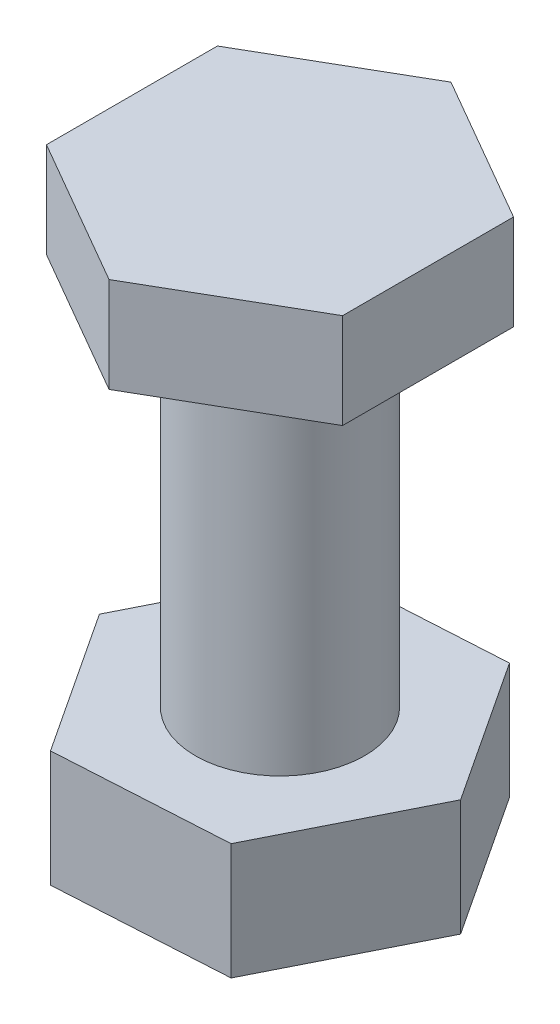
SolidWorks part; units mm, degrees
ref_plane "Front Plane" through (0, 0, 0) normal (0, 0, 1) x (1, 0, 0)
ref_plane "Top Plane" through (0, 0, 0) normal (0, 1, 0) x (1, 0, 0)
ref_plane "Right Plane" through (0, 0, 0) normal (1, 0, 0) x (0, 0, -1)
sketch "Sketch1" plane through (0, 0, 0) normal (0, 1, 0) x (1, 0, 0)
  circle A0 centre (0, 0) radius 3.175
  dimension "D1" = 6.35
extrude "Boss-Extrude1" add sketch "Sketch1" along normal blind 17.1
sketch "Sketch2" plane through (0, 0, 0) normal (0, -1, 0) x (1, 0, 0)
  line L1 (6.4049, -0.3731) -> (3.5256, 5.3603)
  line L2 (3.5256, 5.3603) -> (-2.8794, 5.7334)
  line L3 (-2.8794, 5.7334) -> (-6.4049, 0.3731)
  line L4 (-6.4049, 0.3731) -> (-3.5256, -5.3603)
  line L5 (-3.5256, -5.3603) -> (2.8794, -5.7334)
  line L6 (2.8794, -5.7334) -> (6.4049, -0.3731)
  circle A0 centre (0, 0) radius 5.5563 construction
  dimension "D1" = 11.1125
extrude "Boss-Extrude2" add sketch "Sketch2" along normal blind 4.3656
sketch "Sketch3" plane through (0, 17.1, 0) normal (0, 1, 0) x (1, 0, 0)
  line L1 (0, 6.4158) -> (-5.5562, 3.2079)
  line L2 (-5.5562, 3.2079) -> (-5.5562, -3.2079)
  line L3 (-5.5562, -3.2079) -> (0, -6.4158)
  line L4 (0, -6.4158) -> (5.5563, -3.2079)
  line L5 (5.5563, -3.2079) -> (5.5562, 3.2079)
  line L6 (5.5562, 3.2079) -> (0, 6.4158)
  circle A0 centre (0, 0) radius 5.5562 construction
  dimension "D1" = 11.1125
extrude "Boss-Extrude3" add sketch "Sketch3" against normal blind 3.5719
